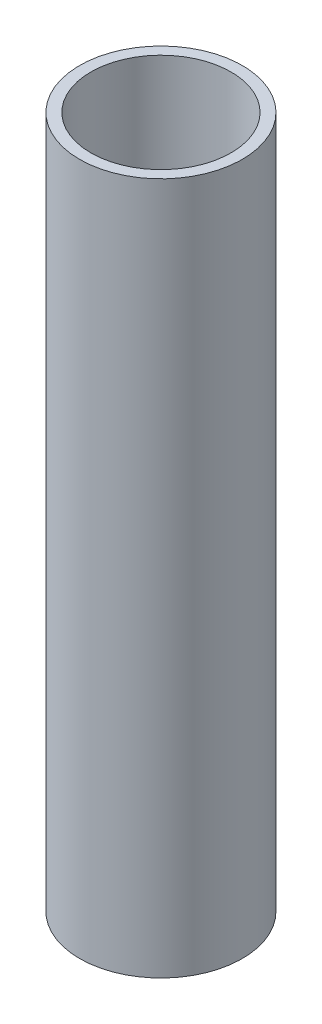
SolidWorks part; units mm, degrees
material "PVC Rigid"
ref_plane "Front Plane" through (0, 0, 0) normal (0, 0, 1) x (1, 0, 0)
ref_plane "Top Plane" through (0, 0, 0) normal (0, 1, 0) x (1, 0, 0)
ref_plane "Right Plane" through (0, 0, 0) normal (1, 0, 0) x (0, 0, -1)
sketch "Sketch2" plane through (0, 0, 0) normal (0, 1, 0) x (1, 0, 0)
  circle A0 centre (0, 0) radius 30.1625
  circle A1 centre (0, 0) radius 25.9969
  dimension "D1" = 60.325
  dimension "D2" = 51.9938
extrude "Boss-Extrude1" add sketch "Sketch2" along normal blind 256.625
